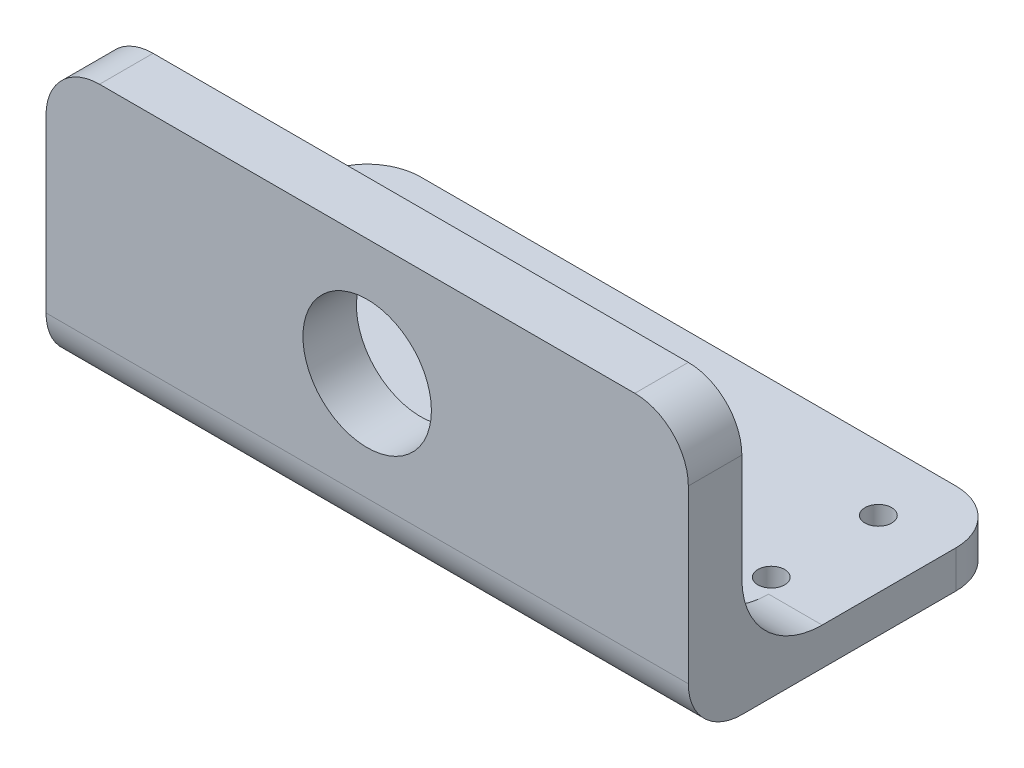
SolidWorks part; units mm, degrees
ref_plane "前视基准面" through (0, 0, 0) normal (0, 0, 1) x (1, 0, 0)
ref_plane "上视基准面" through (0, 0, 0) normal (0, 1, 0) x (1, 0, 0)
ref_plane "右视基准面" through (0, 0, 0) normal (1, 0, 0) x (0, 0, -1)
other "Configuration Table"
ref_plane "基准面1" through (0, -10, 0) normal (0, 1, 0) x (1, 0, 0)
sketch "草图1" plane through (0, -10, 0) normal (0, 1, 0) x (1, 0, 0)
  line L0 (60, 62.5) -> (-60, 62.5)
  line L1 (-60, 62.5) -> (-60, 2.5)
  line L2 (-60, 2.5) -> (60, 2.5)
  line L3 (60, 2.5) -> (60, 62.5)
  dimension "D1" = 120
  dimension "D2" = 60
extrude "凸台-拉伸1" add sketch "草图1" against normal blind 62
sketch "草图3" plane through (0, -10, 0) normal (0, 1, 0) x (1, 0, 0)
  line L0 (60, 2.5) -> (60, 62.5) construction
  line L1 (-60, 62.5) -> (60, 62.5)
  line L2 (-60, 62.5) -> (-60, 12.5)
  line L3 (-60, 12.5) -> (60, 12.5)
  line L4 (60, 62.5) -> (60, 12.5)
  dimension "D1" = 50
extrude "切除-拉伸1" cut sketch "草图3" against normal blind 40
sketch "草图4" plane through (60, 0, 0) normal (1, 0, 0) x (0, 0, -1)
  line L1 (12.5, -50) -> (62.5, -50) construction
  line L2 (27.5, -65) -> (62.5, -65)
  line L3 (62.5, -72) -> (62.5, -50) construction
  line L4 (62.5, -65) -> (62.5, -50)
  line L5 (62.5, -50) -> (12.5, -50)
  arc A0 (12.5, -50) -> (27.5, -65) centre (27.5, -50) ccw
extrude "切除-拉伸2" cut sketch "草图4" against normal through all
ref_plane "对称基准面" through (0, 0, 0) normal (1, 0, 0) x (0, 0, -1)
sketch "草图6" plane through (0, 0, 0) normal (1, 0, 0) x (0, 0, -1)
  line L0 (12.5, -50) -> (12.5, -65)
  line L1 (12.5, -65) -> (27.5, -65)
  line L2 (27.5, -65) -> (12.5, -50)
extrude "切除-拉伸3" cut sketch "草图6" against normal mid plane 100
sketch "草图7" plane through (0, 0, -12.5) normal (0, 0, -1) x (-1, 0, 0)
  line L0 (0, 33) -> (0, -33) construction
  line L1 (-60, -72) -> (60, -72) construction
  circle A0 centre (0, -41.8) radius 12
  dimension "D1" = 30.2
extrude "切除-拉伸4" cut sketch "草图7" against normal mid plane 100
sketch "草图8" plane through (0, -10, 0) normal (0, 1, 0) x (1, 0, 0)
  line L4 (60, 12.5) -> (-60, 12.5)
  line L5 (-60, 12.5) -> (-60, 2.5)
  line L6 (-60, 2.5) -> (60, 2.5)
  line L7 (60, 2.5) -> (60, 12.5)
  line L8 (60, 12.5) -> (-60, 12.5)
  line L9 (-60, 12.5) -> (-60, 2.5)
  line L10 (-60, 2.5) -> (60, 2.5)
  line L11 (60, 2.5) -> (60, 12.5)
  dimension "D1" = 0
extrude "切除-拉伸5" cut sketch "草图8" against normal blind 10
fillet "圆角1" radius 10 2 edges at (60, -20, -7.5) (-60, -20, -7.5)
fillet "圆角2" radius 10 2 edges at (60, -68.5, -62.5) (-60, -68.5, -62.5)
fillet "圆角3" radius 10 1 edges at (0, -72, -2.5)
sketch "草图9" plane through (0, -65, 0) normal (0, 1, 0) x (1, 0, 0)
  line L0 (-50, 62.5) -> (50, 62.5) construction
  line L1 (0, -23.1) -> (0, 23.1) construction
  circle A0 centre (47.5, 50.5) radius 2.5
  circle A1 centre (47.5, 30.5) radius 2.5
  circle A2 centre (-47.5, 50.5) radius 2.5
  circle A3 centre (-47.5, 30.5) radius 2.5
  dimension "D1" = 12
  dimension "D2" = 20
  dimension "D3" = 47.5
extrude "切除-拉伸6" cut sketch "草图9" against normal blind 10
